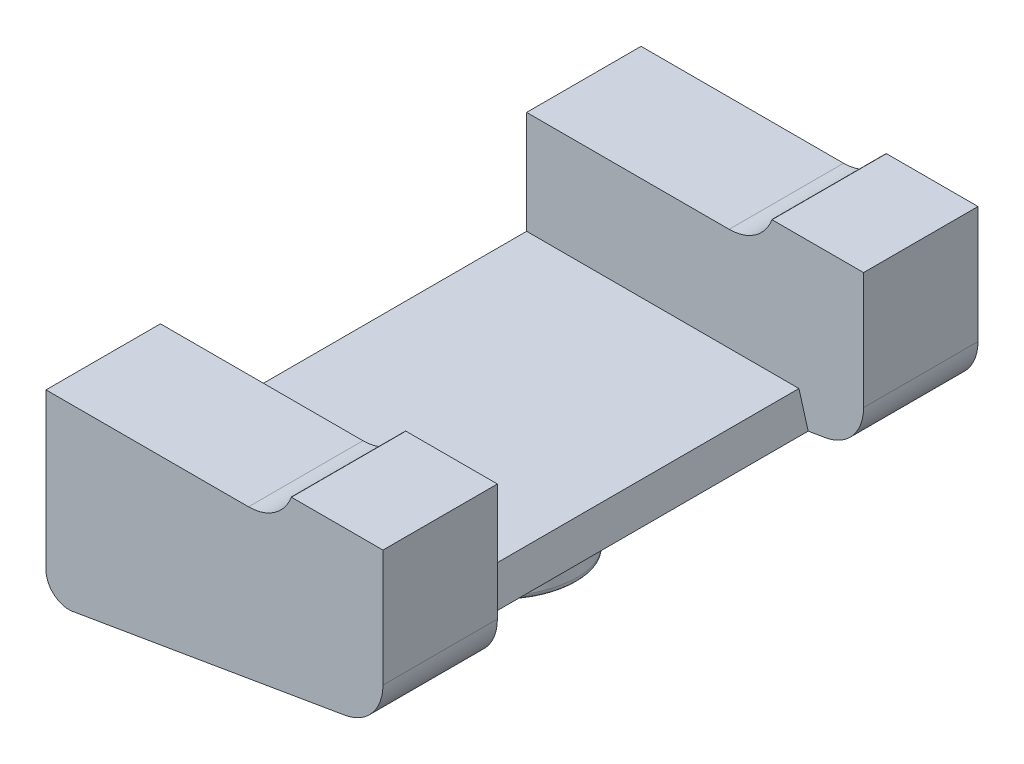
SolidWorks part; units mm, degrees
material "PLA"
ref_plane "Front Plane" through (0, 0, 0) normal (0, 0, 1) x (1, 0, 0)
ref_plane "Top Plane" through (0, 0, 0) normal (0, 1, 0) x (1, 0, 0)
ref_plane "Right Plane" through (0, 0, 0) normal (1, 0, 0) x (0, 0, -1)
sketch "Sketch1" plane through (0, 0, 0) normal (0, 0, 1) x (1, 0, 0)
  line L1 (0, 0) -> (0, -25.5549)
  line L2 (0, 0) -> (0, 36) construction
  line L3 (0, 36) -> (-73.6122, -6.5) construction
  line L4 (-73.6122, -6.5) -> (-73.6122, -40.5794)
  line L5 (-67.7751, -45.5088) -> (-8.3259, -35.4138)
  line L6 (-73.6122, -6.5) -> (-29.3679, -6.5)
  line L7 (-19.971, 0.0798) -> (-20, 0)
  line L8 (-20, 0) -> (0, 0)
  arc A0 (0, -25.5549) -> (-8.3259, -35.4138) centre (-10, -25.5549) cw
  arc A1 (-29.3679, -6.5) -> (-19.971, 0.0798) centre (-29.3679, 3.5) ccw
  arc A2 (-67.7751, -45.5088) -> (-73.6122, -40.5794) centre (-68.6122, -40.5794) cw
  point P10 (0, -34)
  point P15 (-73.6122, -46.5)
  dimension "D8" = 10
  dimension "D9" = 10
  dimension "D10" = 5
  dimension "D1" = 36
  dimension "D2" = 70
  dimension "D3" = 60
  dimension "D4" = 40
  dimension "D5" = 85
  dimension "D6" = 110
  dimension "D7" = 20
extrude "Boss-Extrude1" add sketch "Sketch1" along normal mid plane 130
sketch "Sketch2" plane through (0, 0, 0) normal (0, 0, 1) x (1, 0, 0)
  line L0 (-20, 0) -> (-19.971, 0.0798) construction
  line L1 (0, -25.5549) -> (0, 0) construction
  line L2 (0, 0) -> (-20, 0) construction
  line L3 (-20, 0) -> (-19.971, 0.0798)
  line L4 (0, -25.5549) -> (0, 0)
  line L5 (0, 0) -> (-20, 0)
  line L6 (-21.617, -2.8185) -> (-12.1021, -36.055)
  line L7 (-67.7751, -45.5088) -> (-8.3259, -35.4138) construction
  line L8 (-12.1021, -36.055) -> (-8.3259, -35.4138)
  arc A0 (-29.3679, -6.5) -> (-19.971, 0.0798) centre (-29.3679, 3.5) ccw construction
  arc A1 (-8.3259, -35.4138) -> (0, -25.5549) centre (-10, -25.5549) ccw construction
  arc A2 (-21.617, -2.8185) -> (-19.971, 0.0798) centre (-29.3679, 3.5) ccw
  arc A3 (-8.3259, -35.4138) -> (0, -25.5549) centre (-10, -25.5549) ccw
extrude "Cut-Extrude1" cut sketch "Sketch2" against normal mid plane 80
sketch "Sketch5" plane through (0, -6.5, 0) normal (0, 1, 0) x (1, 0, 0)
  line L0 (-73.6122, -65) -> (-73.6122, 65) construction
  line L1 (-73.6122, 40) -> (-29.4017, 40)
  line L2 (-73.6122, 40) -> (-73.6122, -40)
  line L3 (-73.6122, -40) -> (-29.3679, -40)
  line L5 (-29.3679, -65) -> (-29.3679, 65) construction
  line L6 (-29.3679, 65) -> (-73.6122, 65) construction
  line L7 (-29.3679, -65) -> (-73.6122, -65) construction
  line L8 (-29.3679, -40) -> (0, -40)
  line L9 (0, -40) -> (0, 40)
  line L10 (0, 40) -> (-29.4017, 40)
  dimension "D1" = 25
  dimension "D2" = 25
extrude "Cut-Extrude4" cut sketch "Sketch5" against normal mid plane 45
sketch "Sketch6" plane through (5.6117, -33.0471, 0) normal (0.1674, -0.9859, 0) x (0.9859, 0.1674, 0)
  line L0 (-17.9673, -40) -> (-17.9673, 40) construction
  circle A0 centre (-42.9673, 0) radius 5
  circle A1 centre (-42.9673, 0) radius 12.5
  point P3 (0, 0)
  dimension "D1" = 10
  dimension "D2" = 25
  dimension "D3" = 25
extrude "Boss-Extrude2" add sketch "Sketch6" along normal blind 12
chamfer "Chamfer1" distance 5 angle 45 1 edges at (-49.0728, -42.333, 0)
fillet "Fillet1" radius 1 3 edges at (-22.4167, -49.9783, 0) (-54.0022, -43.1701, 0) (-48.2358, -47.2624, 0)
sketch "Sketch7" plane through (0, 0, 0) normal (0, 0, 1) x (1, 0, 0)
  line L0 (-47.2313, -53.1778) -> (-22.5841, -48.9924) construction
  circle A0 centre (-34.9077, -48.5493) radius 1
  point P4 (-34.9077, -51.0851)
  dimension "D1" = 2
  dimension "D2" = 2.5
extrude "Cut-Extrude5" cut sketch "Sketch7" against normal through all
